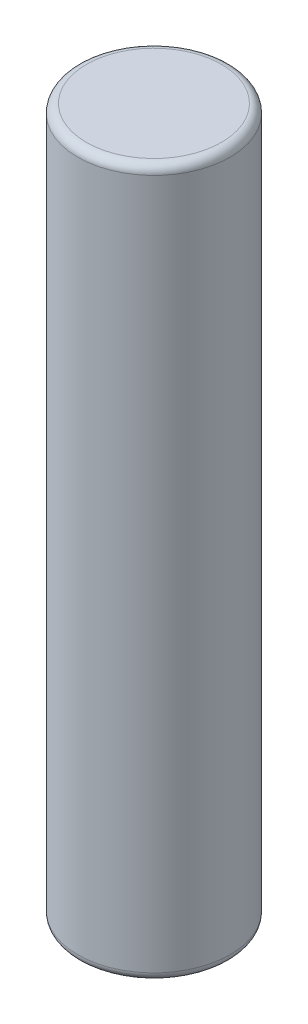
SolidWorks part; units mm, degrees
ref_plane "Front Plane" through (0, 0, 0) normal (0, 0, 1) x (1, 0, 0)
ref_plane "Top Plane" through (0, 0, 0) normal (0, 1, 0) x (1, 0, 0)
ref_plane "Right Plane" through (0, 0, 0) normal (1, 0, 0) x (0, 0, -1)
sketch "Sketch1" plane through (0, 0, 0) normal (0, 1, 0) x (1, 0, 0)
  circle A0 centre (0, 0) radius 1.775
  dimension "D1" = 3.55
extrude "Boss-Extrude1" add sketch "Sketch1" along normal blind 16.5
fillet "Fillet1" radius 0.2 2 edges at (0, 0, 1.775) (0, 16.5, 1.775)
